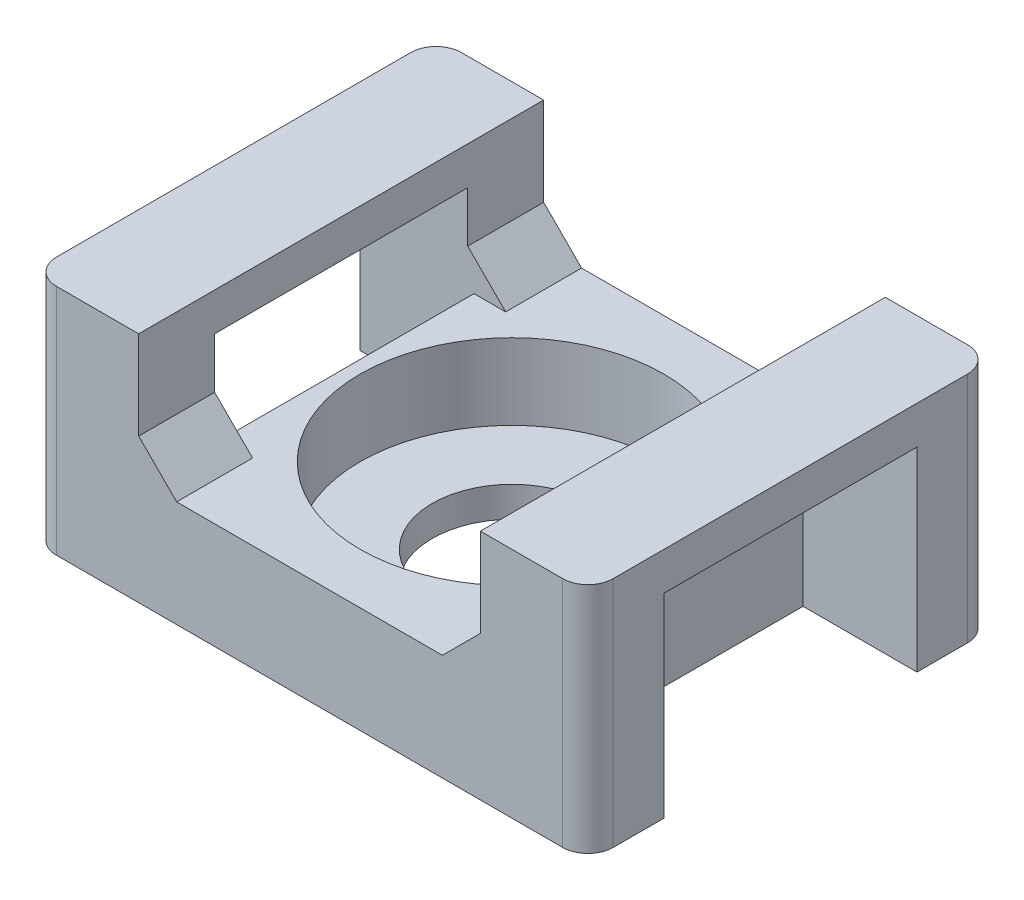
SolidWorks part; units mm, degrees
material "Пластик"
ref_plane "Спереди" through (0, 0, 0) normal (0, 0, 1) x (1, 0, 0)
ref_plane "Сверху" through (0, 0, 0) normal (0, 1, 0) x (1, 0, 0)
ref_plane "Справа" through (0, 0, 0) normal (1, 0, 0) x (0, 0, -1)
sketch "Эскиз1" plane through (0, 0, 0) normal (0, 0, 1) x (1, 0, 0)
  line L7 (11, 0) -> (-11, 0)
  line L8 (-11, 0) -> (-11, 9.2)
  line L9 (-11, 9.2) -> (-6.75, 9.2)
  line L10 (-6.75, 9.2) -> (-6.75, 5.7)
  line L11 (-6.75, 5.7) -> (-5.25, 4.2)
  line L12 (-5.25, 4.2) -> (5.25, 4.2)
  line L13 (0, 4.2) -> (0, 0) construction
  line L14 (6.75, 5.7) -> (5.25, 4.2)
  line L15 (6.75, 9.2) -> (6.75, 5.7)
  line L16 (11, 9.2) -> (6.75, 9.2)
  line L17 (11, 0) -> (11, 9.2)
  point P14 (-5.1092, 4.2)
  dimension "D1" = 22
  dimension "D2" = 13.5
  dimension "D3" = 9.2
  dimension "D4" = 4.2
  dimension "D5" = 135
  dimension "D6" = 1.5
extrude "Бобышка-Вытянуть1" add sketch "Эскиз1" along normal mid plane 16
sketch "Эскиз2" plane through (0, 0, 0) normal (0, 0, 1) x (1, 0, 0)
  line L0 (-11, 7.7) -> (-6.75, 7.7)
  line L1 (-11, 9.2) -> (-11, 0) construction
  line L2 (-6.75, 5.7) -> (-6.75, 9.2) construction
  line L3 (-6.75, 7.7) -> (-6.75, 5.7)
  line L4 (-6.75, 5.7) -> (-5.25, 4.2)
  line L5 (-5.25, 4.2) -> (-6.5, 4.2)
  line L6 (-6.5, 4.2) -> (-6.5, 0)
  line L7 (-11, 0) -> (11, 0) construction
  line L8 (-6.5, 0) -> (-11, 0)
  line L9 (-11, 0) -> (-11, 7.7)
  line L10 (0, 0) -> (0, 4.2) construction
  line L11 (5.25, 4.2) -> (-5.25, 4.2) construction
  dimension "D1" = 7.7
  dimension "D2" = 13
extrude "Вырез-Вытянуть1" cut sketch "Эскиз2" against normal mid plane 10
mirror "Зеркальное отражение1" about plane through (0, 0, 0) normal (1, 0, 0) of "Вырез-Вытянуть1"
hole_wizard "Цековка для  болта с шестигранной головкой M61" positions "Эскиз3" profile "Эскиз5" counterbore size "M6" standard "ISO" end condition up to next
sketch "Эскиз3" plane through (0, 4.2, 0) normal (0, 1, 0) x (1, 0, 0)
  point P0 (0, 0)
sketch "Эскиз5" plane through (0, 4.2, 0) normal (1, 0, 0) x (0, 0, 1)
  line L0 (0, 0) -> (0, 4.2)
  line L1 (0, 4.2) -> (3.15, 4.2)
  line L3 (3.15, 4.2) -> (3.15, 3)
  line L4 (3.15, 3) -> (6, 3)
  line L5 (6, 3) -> (6, 0)
  line L7 (6, 0) -> (0, 0)
  line L11 (0, -6.35) -> (0, 107.95) construction
  dimension "Диаметр сквозного отверстия" = 6.3
  dimension "Глубина сквозного отверстия" = 4.2
  dimension "Диаметр цековки" = 12
  dimension "Глубина цековки" = 3
fillet "Скругление1" radius 1 4 edges at (11, 4.6, -8) (-11, 4.6, -8) (11, 4.6, 8) (-11, 4.6, 8)
